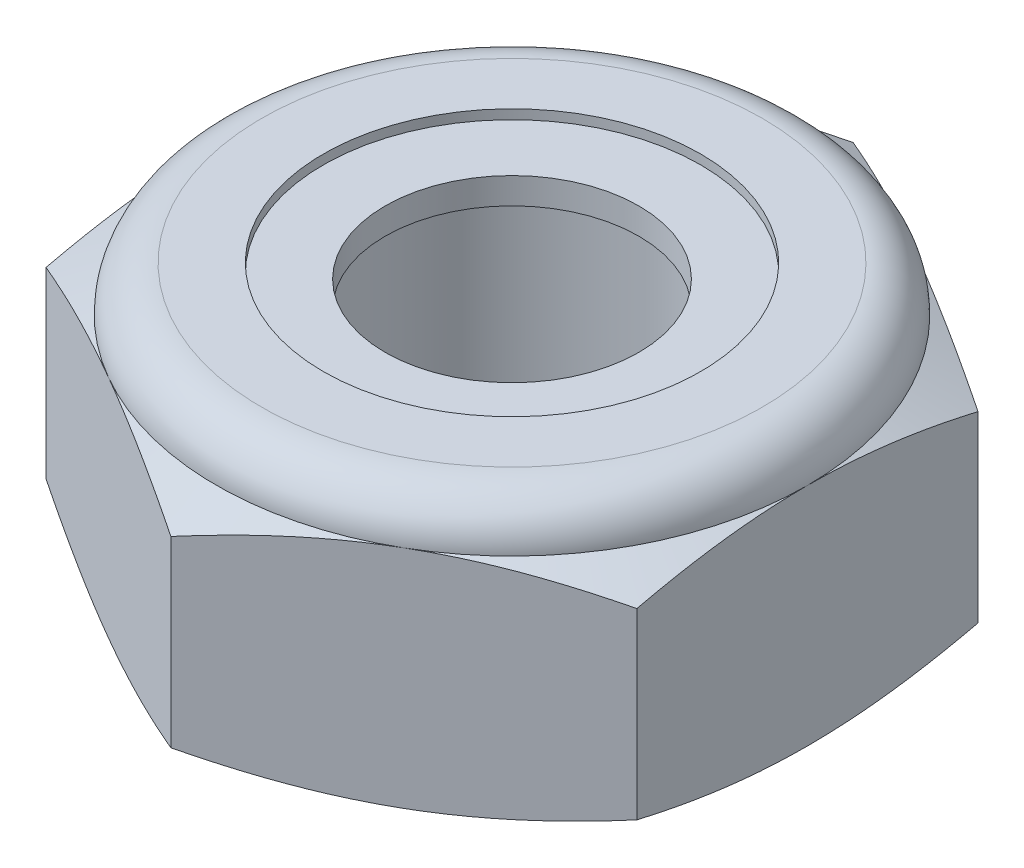
SolidWorks part; units mm, degrees
ref_plane "Front" through (0, 0, 0) normal (0, 0, 1) x (1, 0, 0)
ref_plane "Top" through (0, 0, 0) normal (0, 1, 0) x (1, 0, 0)
ref_plane "Right" through (0, 0, 0) normal (1, 0, 0) x (0, 0, -1)
sketch "Sketch1" plane through (0, 0, 0) normal (0, 1, 0) x (1, 0, 0)
  line L1 (0, 5.4993) -> (-4.7625, 2.7496)
  line L2 (-4.7625, 2.7496) -> (-4.7625, -2.7496)
  line L3 (-4.7625, -2.7496) -> (0, -5.4993)
  line L4 (0, -5.4993) -> (4.7625, -2.7496)
  line L5 (4.7625, -2.7496) -> (4.7625, 2.7496)
  line L6 (4.7625, 2.7496) -> (0, 5.4993)
  circle A0 centre (0, 0) radius 4.7625 construction
  dimension "Hex Flats" = 9.525
extrude "Extrude1" add sketch "Sketch1" along normal blind 4.3656
sketch "Sketch2" plane through (0, 0, 0) normal (1, 0, 0) x (0, 0, -1)
  line L0 (-2.413, 0) -> (-2.413, 4.3656) construction
  line L1 (0, 0) -> (2.413, 0)
  line L2 (0, 0) -> (0, 4.3656)
  line L3 (0, 4.3656) -> (2.413, 4.3656)
  line L4 (2.413, 0) -> (2.413, 4.3656)
  line L5 (-2.7496, 4.3656) -> (2.7496, 4.3656) construction
  line L7 (0, -2.413) -> (0, 0) construction
  dimension "Thread Dia" = 4.826
revolve "Revolve1" add sketch "Sketch2" angle 360 about L7
sketch "Sketch3" plane through (0, 0, 0) normal (1, 0, 0) x (0, 0, -1)
  line L0 (2.413, 4.3656) -> (-2.413, 4.3656) construction
  line L1 (-2.413, 4.3656) -> (-2.413, 3.5719) construction
  line L2 (-2.413, 3.5719) -> (2.413, 4.3656) construction
  line L3 (2.413, 4.3656) -> (2.4291, 4.2677) construction
  line L4 (2.4291, 4.2677) -> (2.5418, 3.5824)
  line L5 (2.5418, 3.5824) -> (2.0776, 3.7574)
  line L6 (2.0776, 3.7574) -> (2.0454, 3.9532)
  line L7 (2.0454, 3.9532) -> (2.4291, 4.2677)
  line L8 (2.0615, 3.8553) -> (2.4855, 3.9251) construction
  line L9 (2.413, 4.3656) -> (2.413, 3.9131) construction
  line L10 (2.413, 3.9131) -> (-2.413, 3.1194) construction
  line L11 (-2.413, 3.1194) -> (-2.413, 3.5719) construction
  line L12 (-0.1397, 4.3656) -> (0.1397, 2.6669) construction
  line L13 (-2.413, 0) -> (-2.413, 4.3656) construction
  line L14 (0, 4.3656) -> (2.413, 4.3656) construction
  line L15 (2.413, 0) -> (2.413, 4.3656) construction
  point P13 (0, 3.5163)
  dimension "D1" = 0.0992
  dimension "D2" = 0.1984
  dimension "Thread Pitch" = 0.7937
  dimension "D4" = 60
  dimension "D5" = 0.7937
sketch "Sketch4" plane through (0, 0, 0) normal (1, 0, 0) x (0, 0, -1)
  line L0 (0, 4.3656) -> (2.413, 4.3656)
  line L1 (2.413, 4.3656) -> (2.0454, 4.1942)
  line L2 (2.0454, 4.1942) -> (2.0454, 0.1714)
  line L3 (2.0454, 0.1714) -> (2.413, 0)
  line L4 (2.413, 0) -> (0, 0)
  line L5 (0, 0) -> (0, 4.3656)
  line L6 (2.413, 0) -> (2.413, 4.3656) construction
  line L7 (0, 4.3656) -> (2.413, 4.3656) construction
  line L8 (0, 0) -> (2.413, 0) construction
  line L9 (0, 0) -> (0, 4.3656) construction
  line L10 (0, 4.3656) -> (0, 4.7712) construction
  dimension "D1" = 25
revolve "Cut-Revolve2" cut sketch "Sketch4" angle 360 about L10
combine bodies "Combine1" operation type subtract main body 112 bodies to subtract 109
sketch "Sketch5" plane through (0, 0, 0) normal (1, 0, 0) x (0, 0, -1)
  line L0 (0, 0) -> (4.7625, 0)
  line L1 (4.7625, 0) -> (5.4993, 0.3436)
  line L2 (5.4993, 0.3436) -> (5.4993, 3.2945)
  line L3 (5.4993, 3.2945) -> (4.7625, 3.638)
  line L4 (4.0349, 4.3656) -> (4.0349, 5.6356)
  line L5 (4.0349, 5.6356) -> (6.7693, 5.6356)
  line L6 (6.7693, 5.6356) -> (6.7693, -1.27)
  line L7 (6.7693, -1.27) -> (0, -1.27)
  line L8 (0, -1.27) -> (0, 0)
  line L9 (4.7625, 3.638) -> (4.7625, 0) construction
  line L10 (0, 0) -> (2.413, 0) construction
  line L13 (5.4993, 1.819) -> (6.7693, 1.819) construction
  line L14 (5.4993, 4.3656) -> (5.4993, 0) construction
  line L15 (0, 0) -> (0, 5.6356) construction
  line L20 (0, 5.6356) -> (4.0349, 5.6356) construction
  line L22 (0, 4.3656) -> (2.413, 4.3656) construction
  arc A0 (4.7625, 3.638) -> (4.0349, 4.3656) centre (4.0349, 3.638) ccw
  dimension "D1" = 25
  dimension "D2" = 1.27
  dimension "D3" = 4.3656
  dimension "D4" = 0.7276
revolve "Cut-Revolve3" cut sketch "Sketch5" angle 360 about L15
sketch "Sketch6" plane through (0, 0, 0) normal (1, 0, 0) x (0, 0, -1)
  line L0 (0, 3.638) -> (4.6101, 3.638)
  line L1 (4.0349, 4.2132) -> (3.0402, 4.2132)
  line L2 (0, 5.6356) -> (0, 3.638)
  line L3 (3.0402, 5.6356) -> (0, 5.6356)
  line L4 (0, 5.6356) -> (4.0349, 5.6356) construction
  line L5 (0, 0) -> (0, 5.6356) construction
  line L6 (0, 5.6356) -> (0, 44.323) construction
  line L7 (3.0402, 4.2132) -> (3.0402, 5.6356)
  line L8 (4.0349, 4.3656) -> (4.0349, 4.2132) construction
  line L9 (3.0402, 4.2132) -> (2.0454, 4.2132) construction
  line L10 (2.0454, 4.2132) -> (2.0454, 4.1942) construction
  arc A0 (4.6101, 3.638) -> (4.0349, 4.2132) centre (4.0349, 3.638) ccw
  arc A1 (4.7625, 3.638) -> (4.0349, 4.3656) centre (4.0349, 3.638) ccw construction
  dimension "D1" = 0.1524
revolve "Cut-Revolve4" cut sketch "Sketch6" angle 360 about L6
sketch "Sketch7" plane through (0, 0, 0) normal (1, 0, 0) x (0, 0, -1)
  line L0 (2.0454, 3.7142) -> (4.528, 3.7142)
  line L1 (4.0349, 4.137) -> (2.0454, 4.137)
  line L2 (2.0454, 4.137) -> (2.0454, 3.7142)
  line L3 (2.0454, 3.7142) -> (0, 3.7142) construction
  line L4 (0, 3.7142) -> (0, 4.137) construction
  line L5 (0, 4.137) -> (2.0454, 4.137) construction
  line L6 (2.0454, 3.7142) -> (2.0454, 3.638) construction
  line L7 (0, 3.638) -> (4.6101, 3.638) construction
  line L8 (4.0349, 4.137) -> (4.0349, 4.2132) construction
  arc A0 (4.528, 3.7142) -> (4.0349, 4.137) centre (4.0349, 3.638) ccw
  arc A2 (4.6101, 3.638) -> (4.0349, 4.2132) centre (4.0349, 3.638) ccw construction
  dimension "D1" = 0.0762
revolve "Revolve2" add sketch "Sketch7" angle 360 about L4
equation "\"D1@Sketch3\"=\"Thread Pitch@Sketch3\"/8"
equation "\"D2@Sketch3\"=\"Thread Pitch@Sketch3\"/4"
equation "\"D5@Sketch3\"=\"Thread Pitch@Sketch3\""
equation "\"D4@Sketch5\"=\"Height@Extrude1\"/6"
